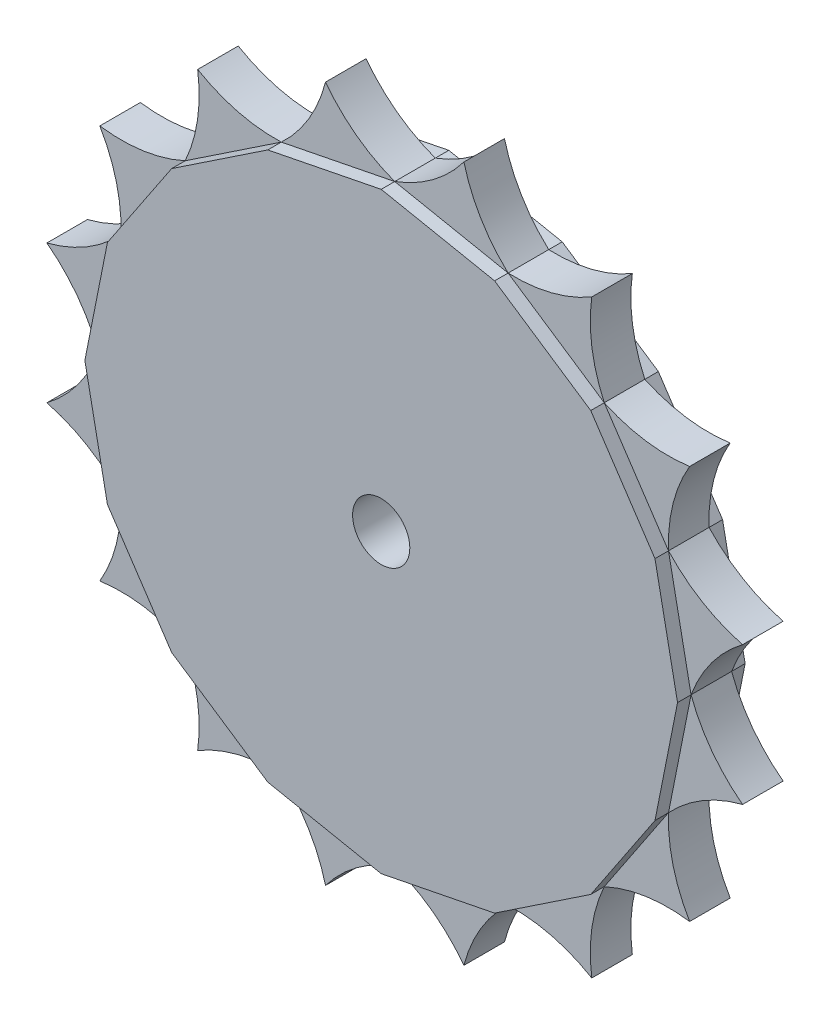
SolidWorks part; units mm, degrees
ref_plane "Ön Düzlem" through (0, 0, 0) normal (0, 0, 1) x (1, 0, 0)
ref_plane "Üst Düzlem" through (0, 0, 0) normal (0, 1, 0) x (1, 0, 0)
ref_plane "Sağ Düzlem" through (0, 0, 0) normal (1, 0, 0) x (0, 0, -1)
sketch "Çizim1" plane through (0, 0, 0) normal (0, 0, 1) x (1, 0, 0)
  line L0 (22.431, 0) -> (-22.431, 0) construction
  line L1 (20.0825, 0) -> (18.4138, 8.3889)
  line L2 (18.4138, 8.3889) -> (13.6619, 15.5006)
  line L3 (13.6619, 15.5006) -> (6.5502, 20.2526)
  line L4 (6.5502, 20.2526) -> (-1.8387, 21.9212)
  line L5 (-1.8387, 21.9212) -> (-10.2276, 20.2526)
  line L6 (-10.2276, 20.2526) -> (-17.3393, 15.5006)
  line L7 (-17.3393, 15.5006) -> (-22.0913, 8.3889)
  line L8 (-22.0913, 8.3889) -> (-23.7599, 0)
  line L9 (-23.7599, 0) -> (-22.0913, -8.3889)
  line L10 (-22.0913, -8.3889) -> (-17.3393, -15.5006)
  line L11 (-17.3393, -15.5006) -> (-10.2276, -20.2526)
  line L12 (-10.2276, -20.2526) -> (-1.8387, -21.9212)
  line L13 (-1.8387, -21.9212) -> (6.5502, -20.2526)
  line L14 (6.5502, -20.2526) -> (13.6619, -15.5006)
  line L15 (13.6619, -15.5006) -> (18.4138, -8.3889)
  line L16 (18.4138, -8.3889) -> (20.0825, 0)
  circle A0 centre (-1.8387, 0) radius 21.5 construction
extrude "Yükseklik-Ekstrüzyon1" add sketch "Çizim1" along normal mid plane 5
sketch "Çizim3" plane through (0, 0, -2.5) normal (0, 0, -1) x (-1, 0, 0)
  line L0 (-13.6619, 15.5006) -> (17.3393, -15.5006) construction
  circle A0 centre (1.8387, 0) radius 2.1165
extrude "Kes-Ekstrüzyon2" cut sketch "Çizim3" against normal blind 31
sketch "Çizim6" plane through (0, 0, 0) normal (0, 0, 1) x (1, 0, 0)
  line L0 (-10.2276, 20.2526) -> (-1.8387, 21.9212)
  line L1 (-1.8387, 21.9212) -> (6.5502, 20.2526)
  line L2 (6.5502, 20.2526) -> (13.6619, 15.5006)
  line L3 (13.6619, 15.5006) -> (18.4138, 8.3889)
  line L4 (18.4138, 8.3889) -> (20.0825, 0)
  line L5 (20.0825, 0) -> (18.4138, -8.3889)
  line L6 (18.4138, -8.3889) -> (13.6619, -15.5006)
  line L7 (13.6619, -15.5006) -> (6.5502, -20.2526)
  line L8 (6.5502, -20.2526) -> (-1.8387, -21.9212)
  line L9 (-1.8387, -21.9212) -> (-10.2276, -20.2526)
  line L10 (-10.2276, -20.2526) -> (-17.3393, -15.5006)
  line L11 (-17.3393, -15.5006) -> (-22.0913, -8.3889)
  line L12 (-22.0913, -8.3889) -> (-23.7599, 0)
  line L13 (-23.7599, 0) -> (-22.0913, 8.3889)
  line L14 (-22.0913, 8.3889) -> (-17.3393, 15.5006)
  line L15 (-17.3393, 15.5006) -> (-10.2276, 20.2526)
  arc A0 (-6.9573, 25.7329) -> (-10.2276, 20.2526) centre (-17.9144, 28.5554) cw
  arc A1 (-6.9573, 25.7329) -> (-1.8387, 21.9212) centre (2.0856, 32.5337) ccw
  arc A2 (3.2799, 25.7329) -> (-1.8387, 21.9212) centre (-5.763, 32.5337) cw
  arc A3 (3.2799, 25.7329) -> (6.5502, 20.2526) centre (14.237, 28.5554) ccw
  arc A4 (12.7378, 21.8153) -> (6.5502, 20.2526) centre (6.9858, 31.559) cw
  arc A5 (12.7378, 21.8153) -> (13.6619, 15.5006) centre (23.941, 20.2299) ccw
  arc A6 (19.9766, 14.5765) -> (13.6619, 15.5006) centre (18.3912, 25.7797) cw
  arc A7 (19.9766, 14.5765) -> (18.4138, 8.3889) centre (29.7202, 8.8245) ccw
  arc A8 (23.8942, 5.1186) -> (18.4138, 8.3889) centre (26.7167, 16.0757) cw
  arc A9 (23.8942, 5.1186) -> (20.0825, 0) centre (30.695, -3.9243) ccw
  arc A10 (23.8942, -5.1186) -> (20.0825, 0) centre (30.695, 3.9243) cw
  arc A11 (23.8942, -5.1186) -> (18.4138, -8.3889) centre (26.7167, -16.0757) ccw
  arc A12 (19.9766, -14.5765) -> (18.4138, -8.3889) centre (29.7202, -8.8245) cw
  arc A13 (19.9766, -14.5765) -> (13.6619, -15.5006) centre (18.3912, -25.7797) ccw
  arc A14 (12.7378, -21.8153) -> (13.6619, -15.5006) centre (23.941, -20.2299) cw
  arc A15 (12.7378, -21.8153) -> (6.5502, -20.2526) centre (6.9858, -31.559) ccw
  arc A16 (3.2799, -25.7329) -> (6.5502, -20.2526) centre (14.237, -28.5554) cw
  arc A17 (3.2799, -25.7329) -> (-1.8387, -21.9212) centre (-5.763, -32.5337) ccw
  arc A18 (-6.9573, -25.7329) -> (-1.8387, -21.9212) centre (2.0856, -32.5337) cw
  arc A19 (-6.9573, -25.7329) -> (-10.2276, -20.2526) centre (-17.9144, -28.5554) ccw
  arc A20 (-16.4152, -21.8153) -> (-10.2276, -20.2526) centre (-10.6632, -31.559) cw
  arc A21 (-16.4152, -21.8153) -> (-17.3393, -15.5006) centre (-27.6184, -20.2299) ccw
  arc A22 (-23.654, -14.5765) -> (-17.3393, -15.5006) centre (-22.0686, -25.7797) cw
  arc A23 (-23.654, -14.5765) -> (-22.0913, -8.3889) centre (-33.3977, -8.8245) ccw
  arc A24 (-27.5716, -5.1186) -> (-22.0913, -8.3889) centre (-30.3941, -16.0757) cw
  arc A25 (-27.5716, -5.1186) -> (-23.7599, 0) centre (-34.3724, 3.9243) ccw
  arc A26 (-27.5716, 5.1186) -> (-23.7599, 0) centre (-34.3724, -3.9243) cw
  arc A27 (-27.5716, 5.1186) -> (-22.0913, 8.3889) centre (-30.3941, 16.0757) ccw
  arc A28 (-23.654, 14.5765) -> (-22.0913, 8.3889) centre (-33.3977, 8.8245) cw
  arc A29 (-23.654, 14.5765) -> (-17.3393, 15.5006) centre (-22.0686, 25.7797) ccw
  arc A30 (-16.4152, 21.8153) -> (-17.3393, 15.5006) centre (-27.6184, 20.2299) cw
  arc A31 (-16.4152, 21.8153) -> (-10.2276, 20.2526) centre (-10.6632, 31.559) ccw
  point P84 (-1.8387, 0)
  dimension "D1" = 16
extrude "Yükseklik-Ekstrüzyon3" add sketch "Çizim6" along normal mid plane 3 contours A1 A0 L0 | A3 A2 L1 | A5 A4 L2 | A7 A6 L3 | A9 A8 L4 | A11 A10 L5 | A13 A12 L6 | A15 A14 L7 | A17 A16 L8 | A19 A18 L9 | A21 A20 L10 | A23 A22 L11 | A25 A24 L12 | A27 A26 L13 | A29 A28 L14 | A31 A30 L15
